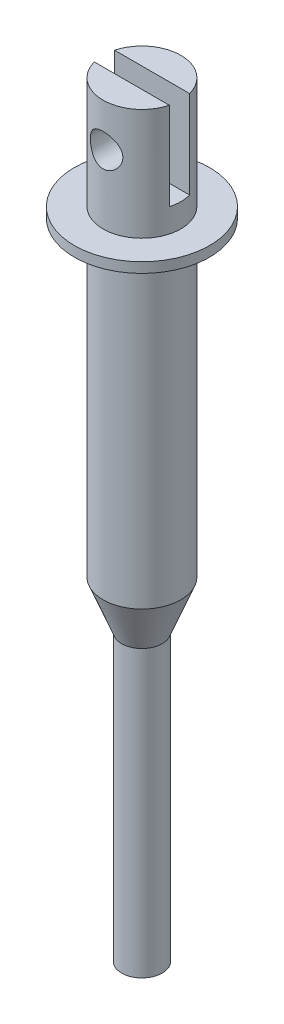
SolidWorks part; units mm, degrees
ref_plane "Front Plane" through (0, 0, 0) normal (0, 0, 1) x (1, 0, 0)
ref_plane "Top Plane" through (0, 0, 0) normal (0, 1, 0) x (1, 0, 0)
ref_plane "Right Plane" through (0, 0, 0) normal (1, 0, 0) x (0, 0, -1)
sketch "Sketch1" plane through (0, 0, 0) normal (0, 0, 1) x (1, 0, 0)
  line L0 (0, 0) -> (1.5, 0)
  line L1 (1.5, 0) -> (1.5, 21.1)
  line L2 (1.5, 21.1) -> (2.875, 24.6)
  line L3 (2.875, 24.6) -> (2.875, 56.6)
  line L4 (2.875, 56.6) -> (0, 56.6)
  line L5 (0, 56.6) -> (0, 0)
  dimension "D1" = 32
  dimension "D2" = 2.875
  dimension "D3" = 1.5
  dimension "D4" = 56.6
  dimension "D5" = 35.5
revolve "Revolve1" add sketch "Sketch1" angle 360 about L5
sketch "Sketch2" plane through (0, 0, 0) normal (0, 0, 1) x (1, 0, 0)
  line L0 (2.875, 56.6) -> (-2.875, 56.6) construction
  line L1 (0, 56.6) -> (0, 54.6) construction
  circle A0 centre (0, 53.4) radius 1.2
  point P2 (0, 54.6)
  dimension "D1" = 2.4
  dimension "D2" = 2
extrude "Cut-Extrude1" cut sketch "Sketch2" against normal through all both and the other way through all
sketch "Sketch3" plane through (0, 56.6, 0) normal (0, 1, 0) x (1, 0, 0)
  line L0 (0, 0) -> (-2.875, 0) construction
  line L5 (-2.875, 0.75) -> (2.875, 0.75)
  line L6 (-2.875, 0.75) -> (-2.875, -0.75)
  line L7 (-2.875, -0.75) -> (2.875, -0.75)
  line L8 (2.875, 0.75) -> (2.875, -0.75)
  circle A1 centre (0, 0) radius 2.875 construction
  dimension "D1" = 1.5
extrude "Cut-Extrude2" cut sketch "Sketch3" against normal blind 6.5
ref_plane "Plane1" through (0, 47.6, 0) normal (0, 1, 0) x (1, 0, 0)
sketch "Sketch4" plane through (0, 47.6, 0) normal (0, 1, 0) x (1, 0, 0)
  circle A0 centre (0, 0) radius 5
  dimension "D1" = 10
extrude "Boss-Extrude1" add sketch "Sketch4" along normal blind 0.75
